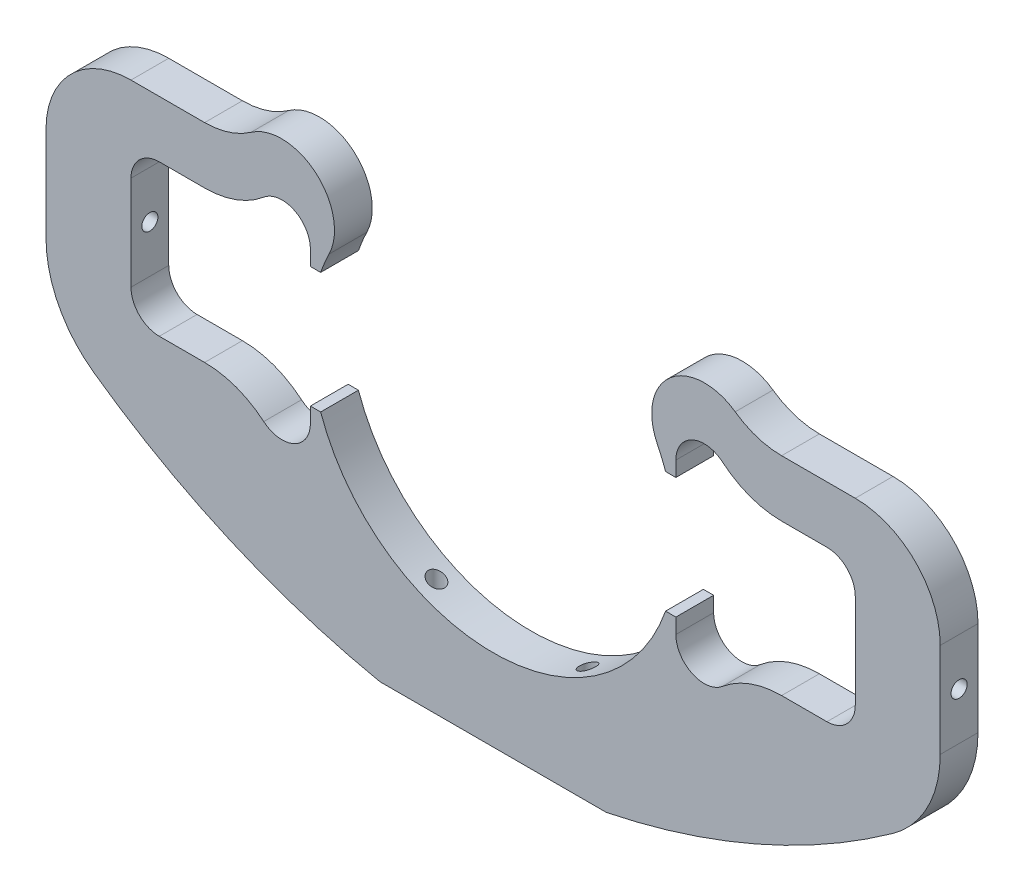
SolidWorks part; units mm, degrees
material "6061-T6 (SS)"
ref_plane "Front Plane" through (0, 0, 0) normal (0, 0, 1) x (1, 0, 0)
ref_plane "Top Plane" through (0, 0, 0) normal (0, 1, 0) x (1, 0, 0)
ref_plane "Right Plane" through (0, 0, 0) normal (1, 0, 0) x (0, 0, -1)
sketch "Sketch1" plane through (0, 0, 0) normal (0, 0, 1) x (1, 0, 0)
  line L0 (-30.725, 12.7) -> (-30.725, 10.16)
  line L1 (-56.125, 12.7) -> (-30.725, 12.7) construction
  line L2 (-56.125, 12.7) -> (-56.125, -12.7) construction
  line L3 (-56.125, -12.7) -> (-30.725, -12.7) construction
  line L4 (-30.725, 12.7) -> (-30.725, -12.7) construction
  line L5 (0, -30.725) -> (0, -44.45)
  line L9 (-60.8875, 7.9375) -> (-60.8875, -7.9375)
  line L10 (-30.725, -12.7) -> (-30.725, -10.16)
  line L15 (-19.05, -44.45) -> (0, -44.45)
  line L16 (-75.175, -7.9375) -> (-75.175, 51.6044) construction
  line L19 (-56.125, -12.7) -> (-48.505, -12.7)
  line L20 (-30.725, 10.16) -> (-28.9966, 10.16)
  line L21 (-75.175, 7.9375) -> (-75.175, -7.9375)
  line L22 (-60.8875, 22.225) -> (-48.505, 22.225)
  line L23 (-30.725, -10.16) -> (-28.9966, -10.16)
  line L24 (-56.125, 12.7) -> (-48.505, 12.7)
  circle A0 centre (0, 0) radius 27.55 construction
  arc A1 (-56.125, 12.7) -> (-60.8875, 7.9375) centre (-56.125, 7.9375) ccw
  arc A2 (-30.725, -12.7) -> (-38.5609, -16.3381) centre (-35.4875, -12.7) cw
  arc A3 (-28.9966, -10.16) -> (0, -30.725) centre (0, 0) ccw
  arc A8 (-75.175, -7.9375) -> (-67.1893, -23.445) centre (-56.125, -7.9375) ccw
  arc A9 (-56.125, -12.7) -> (-60.8875, -7.9375) centre (-56.125, -7.9375) cw
  arc A10 (-48.505, -12.7) -> (-38.5609, -16.3381) centre (-48.505, -28.1093) cw
  circle A11 centre (0, 0) radius 30.725 construction
  arc A12 (-28.9966, 10.16) -> (-27.579, 13.5433) centre (0, 0) cw
  arc A13 (-30.725, 12.7) -> (-38.5609, 16.3381) centre (-35.4875, 12.7) ccw
  arc A14 (-48.505, 12.7) -> (-38.5609, 16.3381) centre (-48.505, 28.1093) ccw
  arc A15 (-27.579, 13.5433) -> (-40.7038, 24.7118) centre (-35.5588, 17.462) ccw
  arc A16 (-48.505, 22.225) -> (-40.7038, 24.7118) centre (-48.505, 35.7045) ccw
  arc A17 (-60.8875, 22.225) -> (-75.175, 7.9375) centre (-60.8875, 7.9375) ccw
  arc A18 (-67.1893, -23.445) -> (-19.05, -44.45) centre (6.573, 79.9384) ccw
  point P12 (-30.725, 0)
  point P15 (0, -44.45)
  dimension "D1" = 55.1
  dimension "D5" = 7.62
  dimension "D6" = 9.525
  dimension "D10" = 19.05
  dimension "D13" = 8.89
  dimension "D7" = 2.54
  dimension "D11" = 4.7625
  dimension "D12" = 127
  dimension "D2" = 25.4
  dimension "D3" = 3.175
  dimension "D4" = 44.45
extrude "Boss-Extrude1" add sketch "Sketch1" along normal blind 6.35
mirror "Mirror1" about plane through (0, -30.725, 6.35) normal (-1, 0, 0) of "Boss-Extrude1"
hole_wizard "#6-32 Tapped Hole2" positions "Sketch3" profile "Sketch2" tap size "#6-32" standard "ANSI Inch" end condition through all
sketch "Sketch3" plane through (0, -44.45, 0) normal (0, -1, 0) x (-1, 0, 0)
  line L0 (-12.7, -3.175) -> (12.7, -3.175) construction
  line L1 (12.7, -3.175) -> (19.05, -3.175) construction
  line L2 (19.05, -6.35) -> (19.05, 0) construction
  line L3 (0, -3.175) -> (0, 0) construction
  point P0 (-12.7, -3.175)
  point P2 (12.7, -3.175)
  dimension "D1" = 25.4
cosmetic thread "Hole Thread4" parameters "D2"=3.5052
cosmetic thread "Hole Thread5" parameters "D2"=3.5052
sketch "Sketch2" plane through (12.7, -44.45, 3.175) normal (1, 0, 0) x (0, 0, -1)
  line L0 (0, 0) -> (0, 70.802)
  line L1 (0, 70.802) -> (1.3525, 70.802)
  line L2 (1.3525, 70.802) -> (1.3525, 0)
  line L5 (1.3525, 0) -> (0, 0)
  line L11 (0, -6.35) -> (0, 107.95) construction
  dimension "Thru Tap Drill Dia." = 2.7051
  dimension "Thru Tap Drill Depth" = 70.802
hole_wizard "#6-32 Tapped Hole1" positions "Sketch5" profile "Sketch4" tap size "#6-32" standard "ANSI Inch" end condition through all
sketch "Sketch5" plane through (-75.175, 0, 0) normal (-1, 0, 0) x (0, 0, 1)
  line L0 (0, -7.9375) -> (6.35, 7.9375) construction
  point P7 (3.175, 0)
sketch "Sketch4" plane through (-75.175, 0, 3.175) normal (0, 1, 0) x (0, 0, 1)
  line L0 (0, 0) -> (0, 150.35)
  line L1 (0, 150.35) -> (1.3525, 150.35)
  line L2 (1.3525, 150.35) -> (1.3525, 0)
  line L5 (1.3525, 0) -> (0, 0)
  line L11 (0, -6.35) -> (0, 107.95) construction
  dimension "Thru Tap Drill Dia." = 2.7051
  dimension "Thru Tap Drill Depth" = 150.35
cosmetic thread "Hole Thread3" parameters "D2"=3.5052
